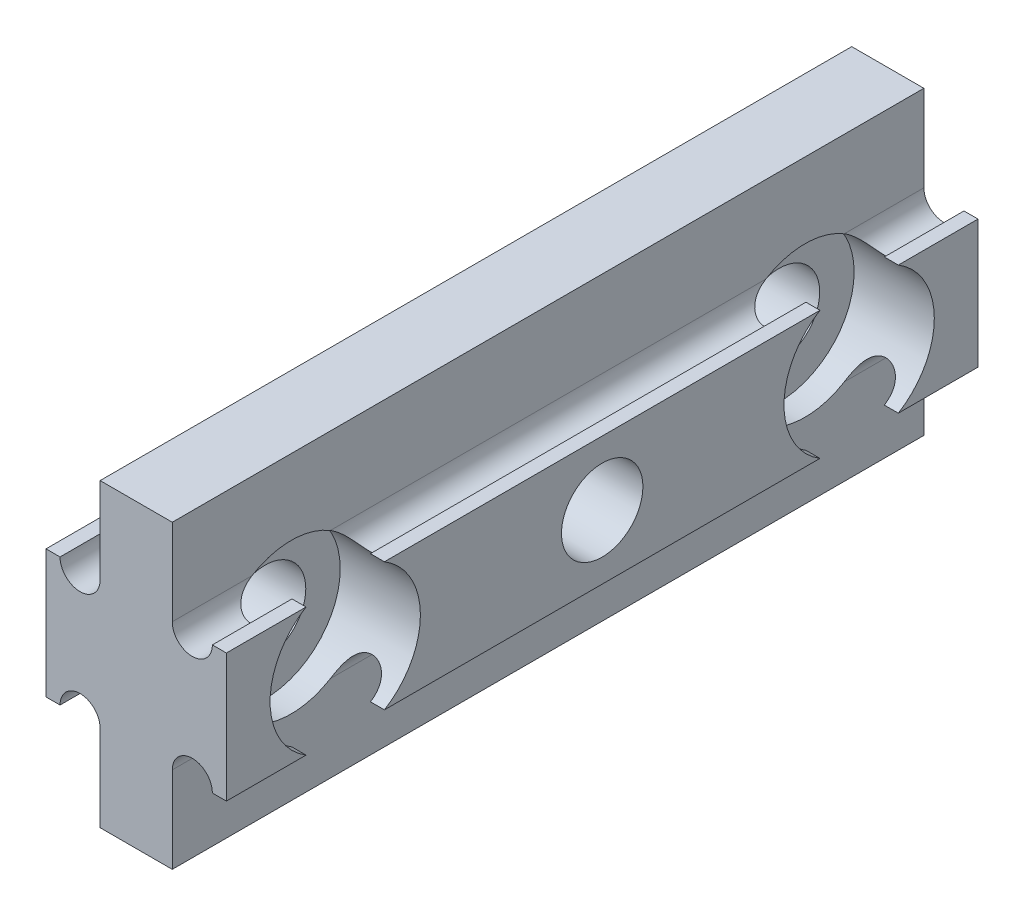
SolidWorks part; units mm, degrees
ref_plane "Front Plane" through (0, 0, 0) normal (0, 0, 1) x (1, 0, 0)
ref_plane "Top Plane" through (0, 0, 0) normal (0, 1, 0) x (1, 0, 0)
ref_plane "Right Plane" through (0, 0, 0) normal (1, 0, 0) x (0, 0, -1)
sketch "Sketch1" plane through (0, 0, 0) normal (0, 0, 1) x (1, 0, 0)
  line L0 (0, -9.525) -> (0, 9.525)
  line L1 (0, 9.525) -> (-2.286, 9.525)
  line L2 (-2.286, 9.525) -> (-2.286, 4.064)
  line L3 (-4.826, 4.064) -> (-5.715, 4.064)
  line L4 (-5.715, 4.064) -> (-5.715, -4.064)
  line L5 (-5.715, 0) -> (0, 0) construction
  line L6 (-4.826, -4.064) -> (-5.715, -4.064)
  line L7 (-2.286, -9.525) -> (-2.286, -4.064)
  line L8 (0, -9.525) -> (-2.286, -9.525)
  arc A0 (-2.286, 4.064) -> (-4.826, 4.064) centre (-3.556, 4.064) cw
  arc A1 (-2.286, -4.064) -> (-4.826, -4.064) centre (-3.556, -4.064) ccw
  point P7 (-5.0158, 4.3611)
  dimension "D1" = 9.525
  dimension "D2" = 1.27
  dimension "D3" = 3.429
  dimension "D4" = 2.286
  dimension "D5" = 4.064
extrude "Boss-Extrude1" add sketch "Sketch1" along normal mid plane 47.625
mirror "Mirror1" about plane through (0, -9.525, 23.8125) normal (-1, 0, 0) of "Boss-Extrude1"
sketch "Sketch2" plane through (5.715, 0, 0) normal (1, 0, 0) x (0, 0, -1)
  line L0 (-16.2814, 0) -> (16.2814, 0) construction
  circle A0 centre (-16.2814, 0) radius 2.5797
  circle A1 centre (16.2814, 0) radius 2.5797
  circle A2 centre (0, 0) radius 2.5797
  dimension "D1" = 5.1594
  dimension "D2" = 32.5628
extrude "Cut-Extrude1" cut sketch "Sketch2" against normal through all
sketch "Sketch3" plane through (5.715, 0, 0) normal (1, 0, 0) x (0, 0, -1)
  circle A0 centre (-16.2814, 0) radius 4.7625
  circle A1 centre (16.2814, 0) radius 4.7625
  dimension "D1" = 9.525
extrude "Cut-Extrude2" cut sketch "Sketch3" against normal blind 5.08
